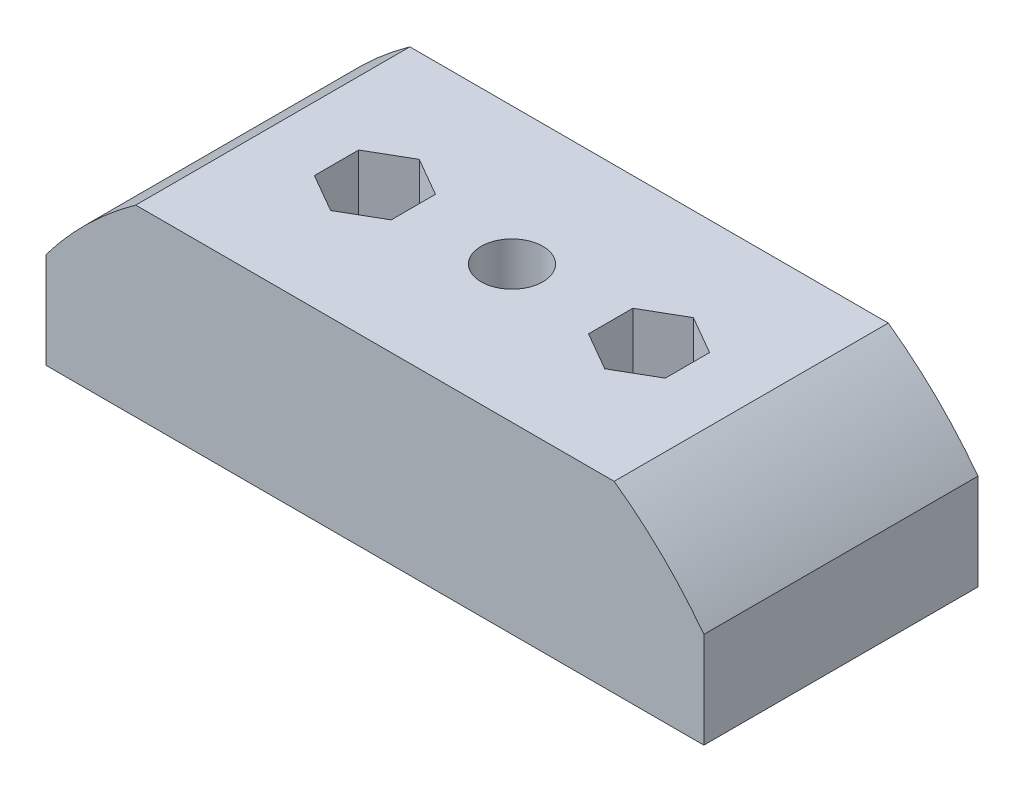
SolidWorks part; units mm, degrees
ref_plane "Front Plane" through (0, 0, 0) normal (0, 0, 1) x (1, 0, 0)
ref_plane "Top Plane" through (0, 0, 0) normal (0, 1, 0) x (1, 0, 0)
ref_plane "Right Plane" through (0, 0, 0) normal (1, 0, 0) x (0, 0, -1)
sketch "Sketch1" plane through (0, 0, 0) normal (0, 0, 1) x (1, 0, 0)
  line L4 (17.4539, -30.6) -> (-17.4539, -30.6)
  line L5 (24, -44) -> (24, -37)
  line L6 (-24, -44) -> (24, -44)
  line L7 (-24, -37) -> (-24, -44)
  line L8 (17.4539, -30.6) -> (-17.4539, -30.6)
  line L9 (24, -44) -> (24, -37)
  line L10 (-24, -44) -> (24, -44)
  line L11 (-24, -37) -> (-24, -44)
  arc A2 (-17.4539, -30.6) -> (-24, -37) centre (0, -55) ccw
  arc A3 (24, -37) -> (17.4539, -30.6) centre (0, -55) ccw
  arc A4 (-17.4539, -30.6) -> (-24, -37) centre (0, -55) ccw
  arc A5 (24, -37) -> (17.4539, -30.6) centre (0, -55) ccw
  dimension "D1" = 0
extrude "Boss-Extrude1" add sketch "Sketch1" along normal mid plane 20
sketch "Sketch2" plane through (0, -30.6, 0) normal (0, 1, 0) x (1, 0, 0)
  line L0 (-17.4539, 0) -> (17.4539, 0) construction
  line L1 (-17.4539, -10) -> (-17.4539, 10) construction
  line L2 (17.4539, -10) -> (17.4539, 10) construction
  line L3 (0, 10) -> (0, -10) construction
  line L4 (17.4539, 10) -> (-17.4539, 10) construction
  line L5 (17.4539, -10) -> (-17.4539, -10) construction
  circle A0 centre (0, 0) radius 2.25
  circle A1 centre (-10, 0) radius 1.6
  circle A2 centre (10, 0) radius 1.6
  dimension "D1" = 4.5
  dimension "D2" = 3.2
  dimension "D3" = 20
extrude "Cut-Extrude1" cut sketch "Sketch2" against normal up to next
sketch "Sketch3" plane through (0, -30.6, 0) normal (0, 1, 0) x (1, 0, 0)
  line L0 (0, 10) -> (0, -10) construction
  line L1 (-10, -3.2332) -> (-7.2, -1.6166)
  line L2 (-7.2, -1.6166) -> (-7.2, 1.6166)
  line L3 (-7.2, 1.6166) -> (-10, 3.2332)
  line L4 (-10, 3.2332) -> (-12.8, 1.6166)
  line L5 (-12.8, 1.6166) -> (-12.8, -1.6166)
  line L6 (-12.8, -1.6166) -> (-10, -3.2332)
  line L7 (17.4539, 10) -> (-17.4539, 10) construction
  line L8 (17.4539, -10) -> (-17.4539, -10) construction
  line L9 (10, -3.2332) -> (7.2, -1.6166)
  line L10 (12.8, -1.6166) -> (10, -3.2332)
  line L11 (12.8, 1.6166) -> (12.8, -1.6166)
  line L12 (10, 3.2332) -> (12.8, 1.6166)
  line L13 (7.2, 1.6166) -> (10, 3.2332)
  line L14 (7.2, -1.6166) -> (7.2, 1.6166)
  circle A0 centre (-10, 0) radius 2.8 construction
  dimension "D1" = 5.6
extrude "Cut-Extrude2" cut sketch "Sketch3" against normal offset from surface (7.4 mm away) 6 up to face at (8.4, -44, 0)
sketch "Sketch4" plane through (0, -44, 0) normal (0, -1, 0) x (1, 0, 0)
  line L1 (0, -4.0415) -> (3.5, -2.0207)
  line L2 (3.5, -2.0207) -> (3.5, 2.0207)
  line L3 (3.5, 2.0207) -> (0, 4.0415)
  line L4 (0, 4.0415) -> (-3.5, 2.0207)
  line L5 (-3.5, 2.0207) -> (-3.5, -2.0207)
  line L6 (-3.5, -2.0207) -> (0, -4.0415)
  circle A0 centre (0, 0) radius 3.5 construction
  dimension "D1" = 7
extrude "Cut-Extrude3" cut sketch "Sketch4" against normal offset from surface (7.4 mm away) 6 up to face at (10, -30.6, 0)
